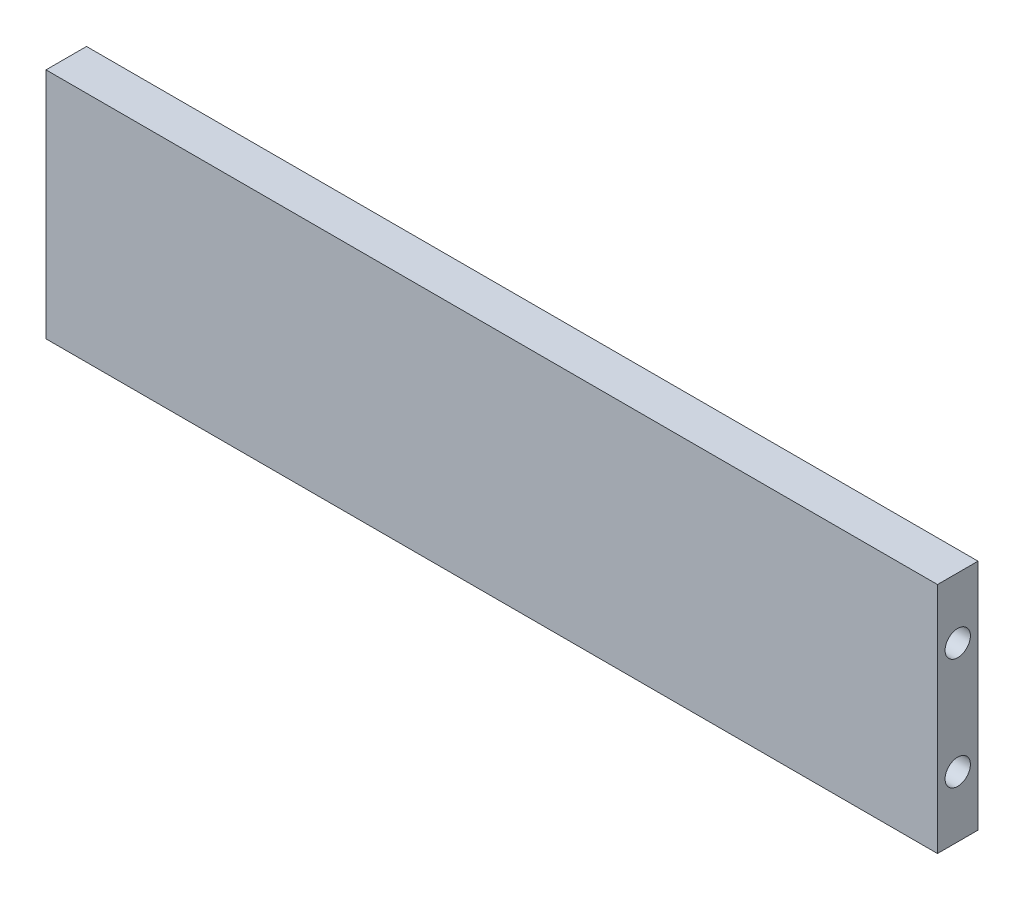
SolidWorks part; units mm, degrees
material "7050-T7651"
ref_plane "Plano frontal" through (0, 0, 0) normal (0, 0, 1) x (1, 0, 0)
ref_plane "Plano superior" through (0, 0, 0) normal (0, 1, 0) x (1, 0, 0)
ref_plane "Plano direito" through (0, 0, 0) normal (1, 0, 0) x (0, 0, -1)
sketch "Esboço1" plane through (0, 0, 0) normal (0, 0, 1) x (1, 0, 0)
  line L1 (0, 0) -> (88.01, 0)
  line L2 (0, 0) -> (0, -23)
  line L3 (0, -23) -> (88.01, -23)
  line L4 (88.01, 0) -> (88.01, -23)
  dimension "D1" = 88.01
  dimension "D2" = 23
extrude "Ressalto-extrusão1" add sketch "Esboço1" along normal blind 4
sketch "Esboço2" plane through (0, 0, 0) normal (-1, 0, 0) x (0, 0, 1)
  line L0 (2, 0) -> (2, -23) construction
  line L1 (4, 0) -> (0, 0) construction
  line L2 (4, -23) -> (0, -23) construction
  circle A0 centre (2, -6) radius 1.25
  circle A1 centre (2, -17) radius 1.25
  dimension "D1" = 2.5
  dimension "D2" = 2.5
  dimension "D3" = 6
  dimension "D4" = 6
extrude "Corte-extrusão1" cut sketch "Esboço2" against normal blind 10
sketch "Esboço3" plane through (88.01, 0, 0) normal (1, 0, 0) x (0, 0, -1)
  line L0 (-2, 0) -> (-2, -23) construction
  line L1 (-4, 0) -> (0, 0) construction
  line L2 (-4, -23) -> (0, -23) construction
  circle A0 centre (-2, -6) radius 1.25
  circle A1 centre (-2, -17) radius 1.25
  dimension "D1" = 2.5
  dimension "D2" = 2.5
  dimension "D3" = 6
  dimension "D4" = 6
extrude "Corte-extrusão2" cut sketch "Esboço3" against normal blind 10
